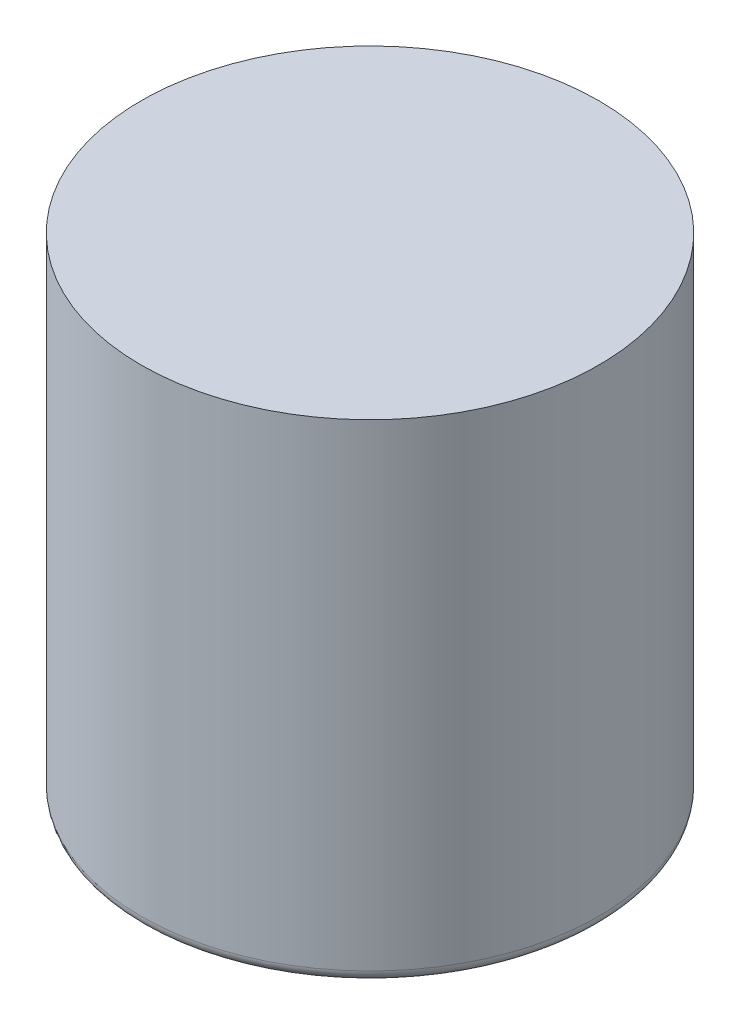
SolidWorks part; units mm, degrees
ref_plane "Front Plane" through (0, 0, 0) normal (0, 0, 1) x (1, 0, 0)
ref_plane "Top Plane" through (0, 0, 0) normal (0, 1, 0) x (1, 0, 0)
ref_plane "Right Plane" through (0, 0, 0) normal (1, 0, 0) x (0, 0, -1)
sketch "Sketch1" plane through (0, 0, 0) normal (0, 1, 0) x (1, 0, 0)
  circle A0 centre (0, 0) radius 58.5
  dimension "D1" = 117
extrude "Boss-Extrude1" add sketch "Sketch1" along normal blind 125
fillet "Fillet1" radius 3 1 edges at (0, 0, 58.5)
